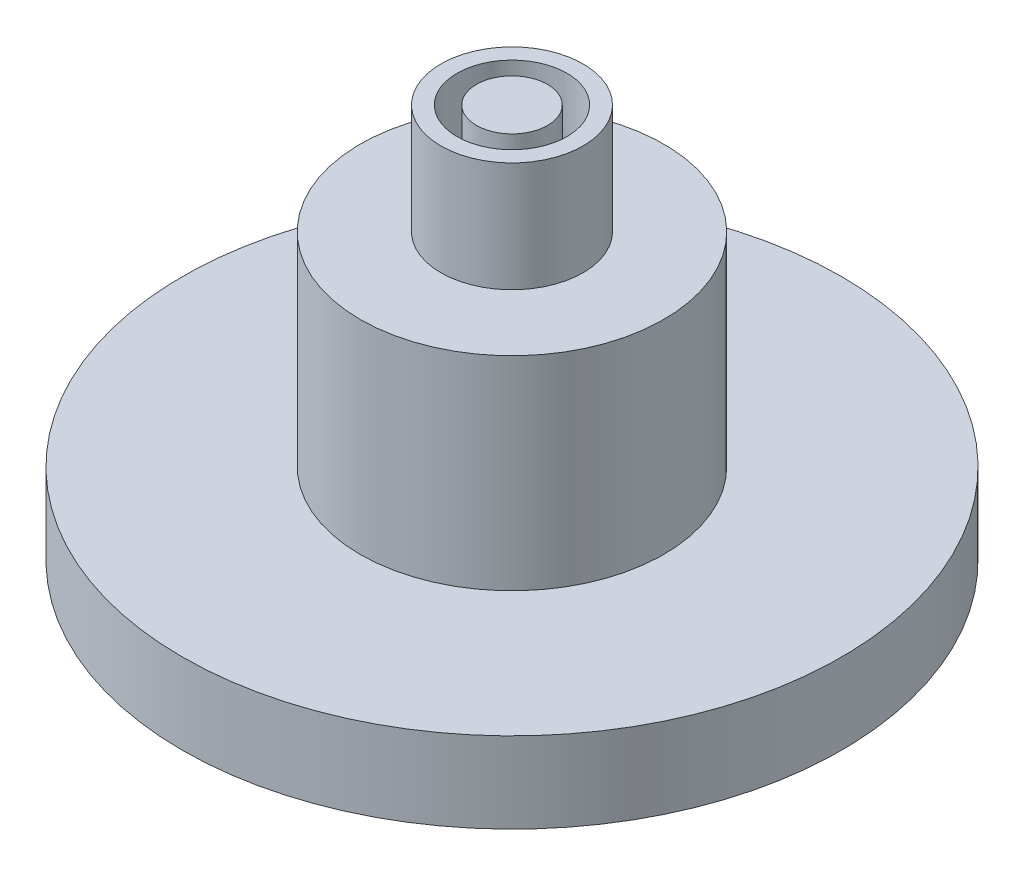
SolidWorks part; units mm, degrees
ref_plane "Front Plane" through (0, 0, 0) normal (0, 0, 1) x (1, 0, 0)
ref_plane "Top Plane" through (0, 0, 0) normal (0, 1, 0) x (1, 0, 0)
ref_plane "Right Plane" through (0, 0, 0) normal (1, 0, 0) x (0, 0, -1)
sketch "Sketch2" plane through (0, 0, 0) normal (0, 1, 0) x (1, 0, 0)
  circle A0 centre (0, 0) radius 12.954
  dimension "D1" = 25.908
extrude "Boss-Extrude1" add sketch "Sketch2" along normal blind 3.175
sketch "Sketch3" plane through (0, 3.175, 0) normal (0, 1, 0) x (1, 0, 0)
  circle A0 centre (0, 0) radius 5.969
  dimension "D1" = 11.938
extrude "Boss-Extrude2" add sketch "Sketch3" along normal blind 8.001
sketch "Sketch4" plane through (0, 11.176, 0) normal (0, 1, 0) x (1, 0, 0)
  circle A0 centre (0, 0) radius 1.397
  circle A1 centre (0, 0) radius 2.159
  circle A2 centre (0, 0) radius 2.794
  dimension "D1" = 2.794
  dimension "D2" = 4.318
  dimension "D3" = 5.588
extrude "Boss-Extrude3" add sketch "Sketch4" along normal blind 4.318 contours A0 | A2 A1
